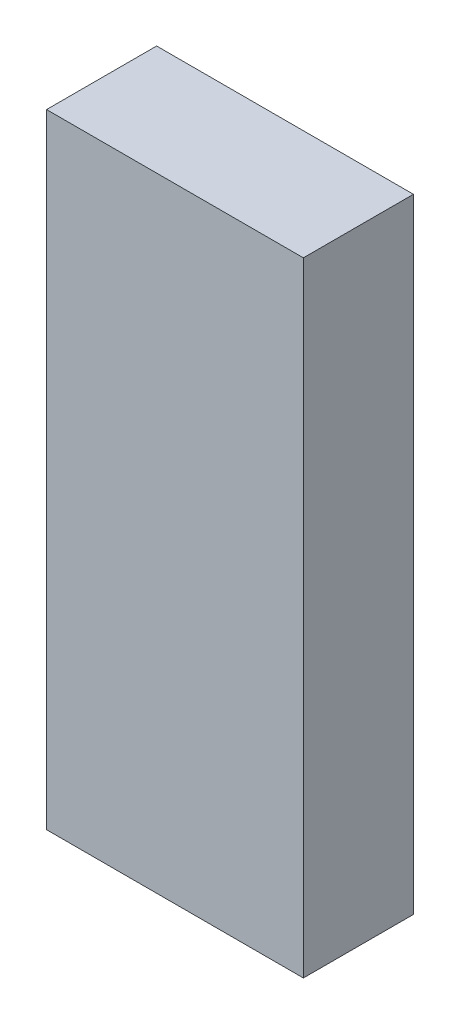
SolidWorks part; units mm, degrees
ref_plane "Front Plane" through (0, 0, 0) normal (0, 0, 1) x (1, 0, 0)
ref_plane "Top Plane" through (0, 0, 0) normal (0, 1, 0) x (1, 0, 0)
ref_plane "Right Plane" through (0, 0, 0) normal (1, 0, 0) x (0, 0, -1)
sketch "Sketch1" plane through (0, 0, 0) normal (0, 1, 0) x (1, 0, 0)
  line L1 (-44.45, 19.05) -> (44.45, 19.05)
  line L2 (-44.45, 19.05) -> (-44.45, -19.05)
  line L3 (-44.45, -19.05) -> (44.45, -19.05)
  line L4 (44.45, 19.05) -> (44.45, -19.05)
  line L5 (-44.45, 19.05) -> (44.45, -19.05) construction
  line L6 (-44.45, -19.05) -> (44.45, 19.05) construction
  point P0 (0, 0)
  dimension "D1" = 88.9
  dimension "D2" = 38.1
extrude "Boss-Extrude1" add sketch "Sketch1" along normal blind 215.9
